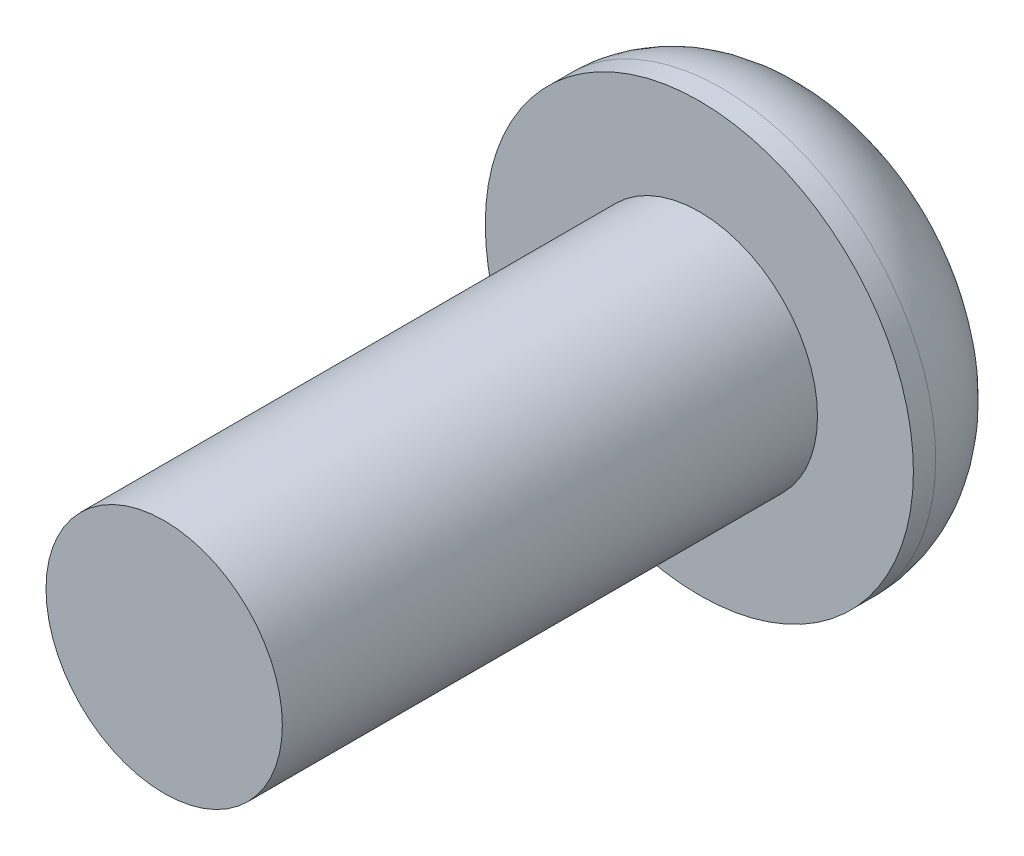
SolidWorks part; units mm, degrees
ref_plane "Front Plane" through (0, 0, 0) normal (0, 0, 1) x (1, 0, 0)
ref_plane "Top Plane" through (0, 0, 0) normal (0, 1, 0) x (1, 0, 0)
ref_plane "Right Plane" through (0, 0, 0) normal (1, 0, 0) x (0, 0, -1)
sketch "Sketch1" plane through (0, 0, 0) normal (0, 0, 1) x (1, 0, 0)
  circle A0 centre (0, 0) radius 3.175
  dimension "D1" = 6.35
extrude "Extrude1" add sketch "Sketch1" along normal blind 1.8542
fillet "Fillet1" radius 1.524 1 edges at (3.175, 0, 0)
sketch "Sketch2" plane through (0, 0, 1.8542) normal (0, 0, 1) x (1, 0, 0)
  circle A0 centre (0, 0) radius 1.7526
  dimension "D1" = 3.5052
extrude "Extrude2" add sketch "Sketch2" along normal blind 7.9375
sketch "Sketch3" plane through (0, 0, 0) normal (0, 0, -1) x (-1, 0, 0)
  line L1 (0.5909, 0.9816) -> (-0.5546, 1.0025)
  line L3 (-0.5546, 1.0025) -> (-1.1455, 0.0209)
  line L5 (-1.1455, 0.0209) -> (-0.5909, -0.9816)
  line L6 (-0.5909, -0.9816) -> (0.5546, -1.0025)
  line L7 (0.5546, -1.0025) -> (1.1455, -0.0209)
  line L8 (1.1455, -0.0209) -> (0.5909, 0.9816)
  circle A1 centre (0, 0) radius 0.9922 construction
  point P0 (0, 0)
  point P8 (0, 0)
extrude "Extrude3" cut sketch "Sketch3" against normal blind 1.016
